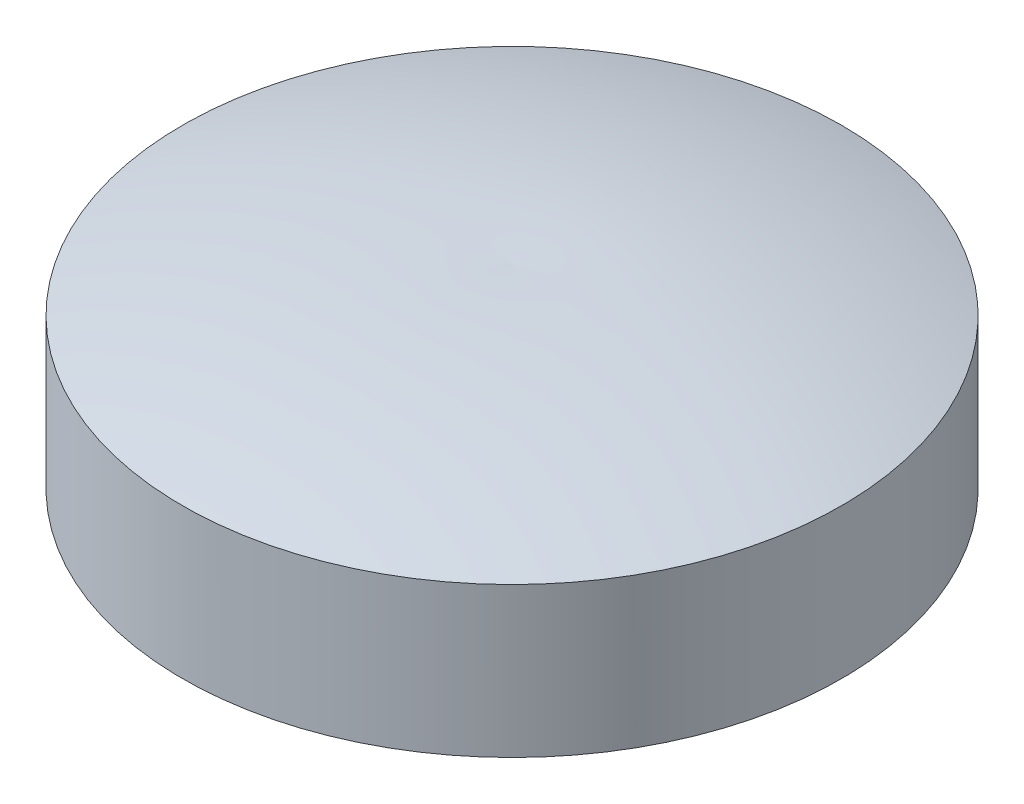
SolidWorks part; units mm, degrees
ref_plane "Front Plane" through (0, 0, 0) normal (0, 0, 1) x (1, 0, 0)
ref_plane "Top Plane" through (0, 0, 0) normal (0, 1, 0) x (1, 0, 0)
ref_plane "Right Plane" through (0, 0, 0) normal (1, 0, 0) x (0, 0, -1)
sketch "Sketch1" plane through (0, 0, 0) normal (0, 0, 1) x (1, 0, 0)
  line L0 (-0.0973, 0.1744) -> (-0.0973, 24.4412) construction
  line L1 (-0.0973, 0.1744) -> (21.9027, 0.1744)
  line L2 (21.9027, 0.1744) -> (21.9027, 10.1744)
  line L3 (-0.0973, 13.1744) -> (-0.0973, 0.1744)
  arc A0 (-0.0973, 13.1744) -> (21.9027, 10.1744) centre (2.6902, -48.5503) cw
  dimension "D2" = 3
  dimension "D1" = 44
  dimension "D3" = 10
revolve "Revolve1" add sketch "Sketch1" angle 360 about L0
sketch "Sketch2" plane through (0, 0.1744, 0) normal (0, -1, 0) x (1, 0, 0)
  line L0 (0, 0) -> (-22.0973, 0) construction
  arc A0 (-22.0462, -1.4991) -> (-22.0462, 1.4991) centre (-22.0973, 0) ccw
  circle A1 centre (-0.0973, 0) radius 22 construction
  arc A2 (-22.0462, 1.4991) -> (-22.0462, -1.4991) centre (-0.0973, 0) ccw
  dimension "D1" = 3
extrude "Cut-Extrude1" cut sketch "Sketch2" against normal blind 5
